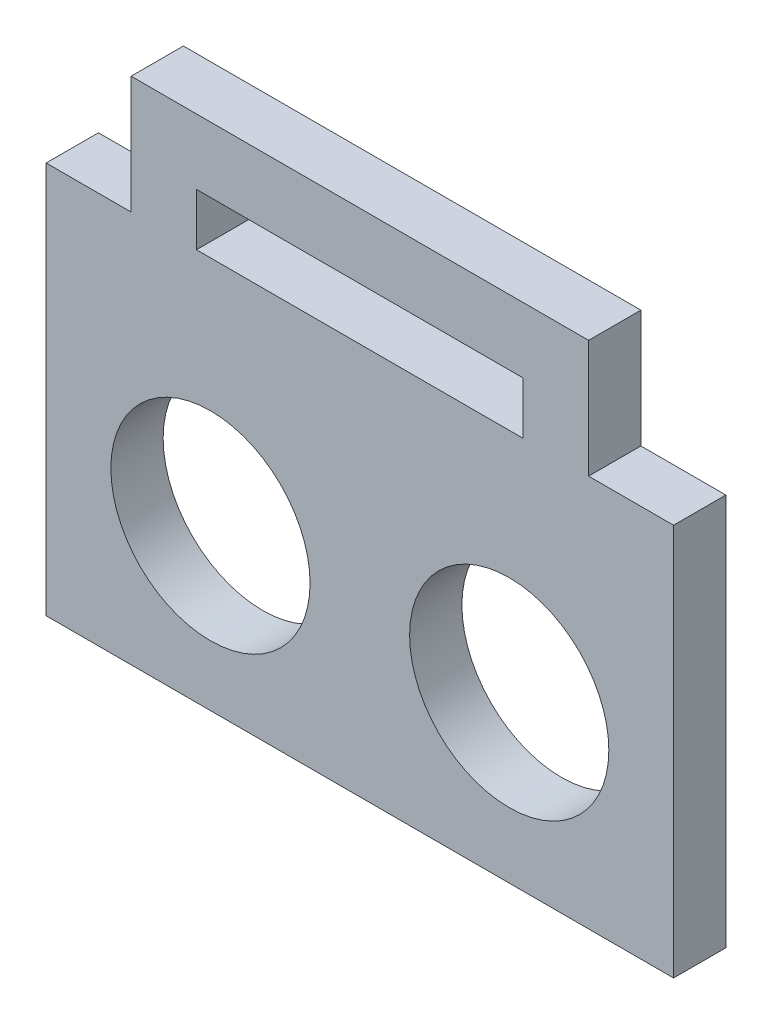
SolidWorks part; units mm, degrees
ref_plane "Přední rovina" through (0, 0, 0) normal (0, 0, 1) x (1, 0, 0)
ref_plane "Horní rovina" through (0, 0, 0) normal (0, 1, 0) x (1, 0, 0)
ref_plane "Pravá rovina" through (0, 0, 0) normal (1, 0, 0) x (0, 0, -1)
sketch "Skica1" plane through (0, 0, 0) normal (0, 0, 1) x (1, 0, 0)
  line L1 (-19.7439, 5.4997) -> (28.2561, 5.4997)
  line L2 (-19.7439, 5.4997) -> (-19.7439, -24.5003)
  line L3 (-19.7439, -24.5003) -> (28.2561, -24.5003)
  line L4 (28.2561, 5.4997) -> (28.2561, -24.5003)
  line L5 (-13.2439, 5.4997) -> (21.7561, 5.4997)
  line L6 (-13.2439, 5.4997) -> (-13.2439, 14.4997)
  line L7 (-13.2439, 14.4997) -> (21.7561, 14.4997)
  line L8 (21.7561, 5.4997) -> (21.7561, 14.4997)
  line L9 (16.7561, 5.4997) -> (-8.2439, 5.4997)
  line L10 (16.7561, 5.4997) -> (16.7561, 9.4997)
  line L11 (16.7561, 9.4997) -> (-8.2439, 9.4997)
  line L12 (-8.2439, 5.4997) -> (-8.2439, 9.4997)
  circle A0 centre (-7.1739, -12.2502) radius 7.62
  circle A1 centre (15.6831, -11.8803) radius 7.62
  dimension "D1" = 22.86
  dimension "D2" = 15.24
  dimension "D3" = 15.24
  dimension "D9" = 12.57
  dimension "D13" = 17.38
  dimension "D4" = 5
  dimension "D5" = 5
  dimension "D6" = 5
  dimension "D7" = 4
  dimension "D8" = 25
  dimension "D10" = 48
  dimension "D11" = 6.5
  dimension "D12" = 30
extrude "Přidat vysunutím1" add sketch "Skica1" along normal blind 4 contours L4 L1 L5 L2 L3 A1 A0 | L1 L12 L11 L10 L8 L7 L6
